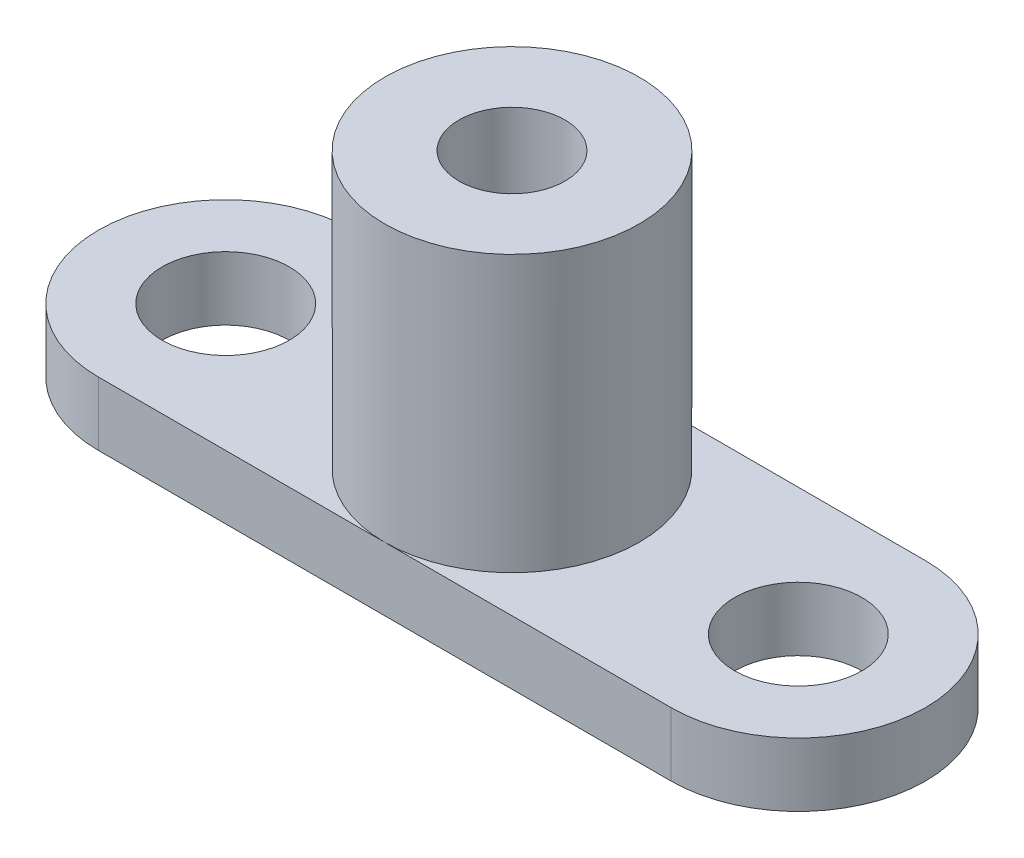
SolidWorks part; units mm, degrees
ref_plane "前视基准面" through (0, 0, 0) normal (0, 0, 1) x (1, 0, 0)
ref_plane "上视基准面" through (0, 0, 0) normal (0, 1, 0) x (1, 0, 0)
ref_plane "右视基准面" through (0, 0, 0) normal (1, 0, 0) x (0, 0, -1)
sketch "草图1" plane through (0, 0, 0) normal (0, 1, 0) x (1, 0, 0)
  line L0 (-13.5, 6) -> (13.5, 6)
  line L1 (-13.5, -6) -> (13.5, -6)
  line L4 (-13.5, 6) -> (-13.5, -6)
  line L8 (13.5, 6) -> (13.5, -6)
  circle A0 centre (-13.5, 0) radius 6
  circle A1 centre (13.5, 0) radius 6
  point P14 (0, 0)
  dimension "D1" = 12
  dimension "D2" = 13.5
  dimension "D3" = 13.5
extrude "凸台-拉伸1" add sketch "草图1" along normal blind 3
sketch "草图2" plane through (0, 3, 0) normal (0, 1, 0) x (1, 0, 0)
  circle A0 centre (0, 0) radius 6
extrude "凸台-拉伸2" add sketch "草图2" along normal blind 13
hole_wizard "M6 螺纹孔1" positions "草图3" profile "草图5" tap size "M6" standard "GB" end condition through all
sketch "草图3" plane through (0, 16, 0) normal (0, 1, 0) x (1, 0, 0)
  point P0 (0, 0)
sketch "草图5" plane through (0, 16, 0) normal (1, 0, 0) x (0, 0, 1)
  line L0 (0, 0) -> (0, 16)
  line L1 (0, 16) -> (2.5, 16)
  line L2 (2.5, 16) -> (2.5, 0)
  line L5 (2.5, 0) -> (0, 0)
  line L11 (0, -6.35) -> (0, 107.95) construction
  dimension "通孔螺纹孔钻头直径" = 5
  dimension "通孔螺纹孔钻头深度" = 16
cosmetic thread "孔螺蚊线1" parameters "D2"=6
sketch "草图6" plane through (0, 3, 0) normal (0, 1, 0) x (1, 0, 0)
  circle A0 centre (-13.5, 0) radius 3
  circle A1 centre (13.5, 0) radius 3
  point P2 (-13.5, 0)
  point P6 (0, 0)
  point P7 (-13.4741, -4.6853)
  point P8 (0, 0)
  point P10 (13.5, 0)
  point P11 (0, 0)
  point P12 (13.5, 0)
  dimension "D1" = 6
  dimension "D2" = 6
extrude "切除-拉伸1" cut sketch "草图6" against normal blind 10
